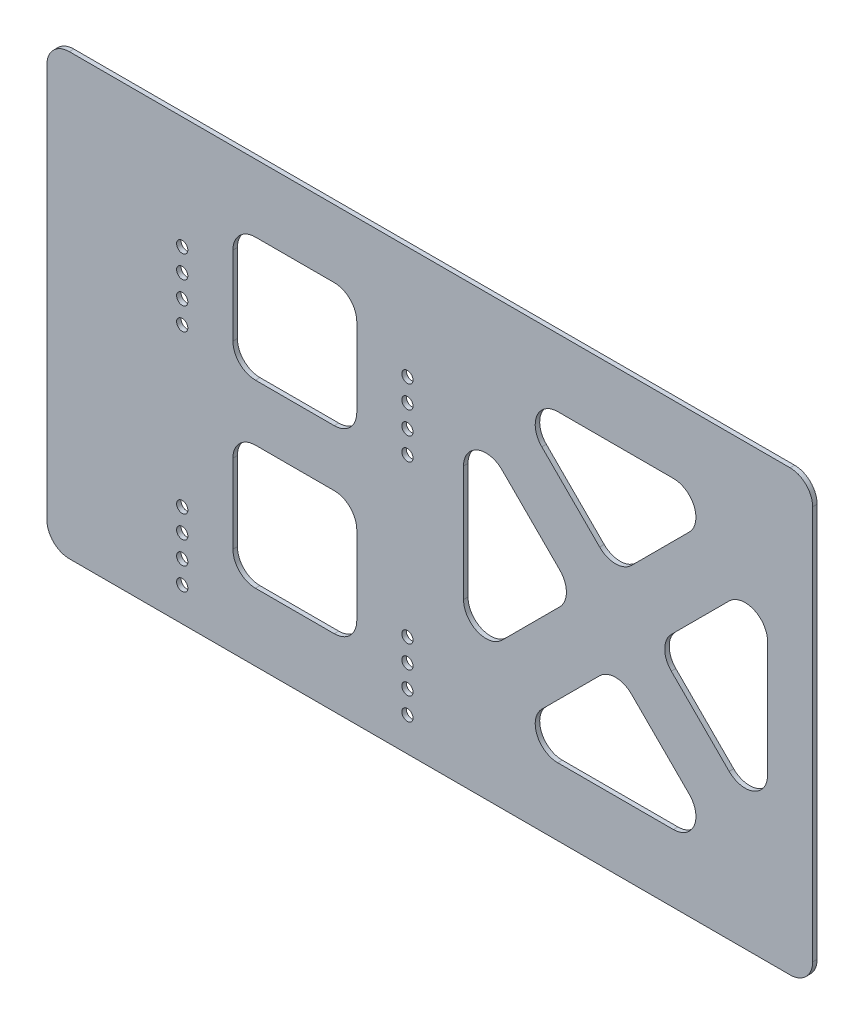
SolidWorks part; units mm, degrees
ref_plane "Front Plane" through (0, 0, 0) normal (0, 0, 1) x (1, 0, 0)
ref_plane "Top Plane" through (0, 0, 0) normal (0, 1, 0) x (1, 0, 0)
ref_plane "Right Plane" through (0, 0, 0) normal (1, 0, 0) x (0, 0, -1)
sketch "Sketch1" plane through (0, 0, 0) normal (0, 0, 1) x (1, 0, 0)
  line L0 (-269.9, 0) -> (-269.9, -1100) construction
  line L1 (-269.9, -292) -> (-609.9, -292)
  line L2 (-269.9, -292) -> (-269.9, -487)
  line L3 (-269.9, -487) -> (-609.9, -487)
  line L4 (-609.9, -292) -> (-609.9, -487)
  line L5 (-609.9, -1100) -> (-609.9, 0) construction
  line L6 (-589.9, -292) -> (-289.9, -292) construction
  dimension "D1" = 195
extrude "Boss-Extrude1" add sketch "Sketch1" along normal blind 2
sketch "Sketch2" plane through (0, 0, 2) normal (0, 0, 1) x (1, 0, 0)
  line L0 (-609.9, -412) -> (-269.9, -412) construction
  line L1 (-609.9, -292) -> (-609.9, -487) construction
  line L2 (-269.9, -487) -> (-269.9, -292) construction
  line L3 (-269.9, -292) -> (-609.9, -292) construction
  line L4 (-449.8, -487) -> (-449.8, -292) construction
  line L5 (-609.9, -487) -> (-269.9, -487) construction
  line L6 (-549.8, -292) -> (-549.8, -487) construction
  line L17 (-549.8, -292) -> (-449.8, -292) construction
  line L18 (-449.8, -462) -> (-549.8, -462) construction
  line L19 (-549.8, -462) -> (-549.8, -362) construction
  line L20 (-549.8, -362) -> (-449.8, -362) construction
  circle A0 centre (-449.8, -362) radius 2.5
  circle A1 centre (-449.8, -462) radius 2.5
  circle A2 centre (-549.8, -462) radius 2.5
  circle A3 centre (-549.8, -362) radius 2.5
  point P14 (-499.8, -292)
  point P21 (-549.8, -412)
  dimension "D4" = 5
  dimension "D1" = 120
  dimension "D2" = 100
  dimension "D3" = 110.1
extrude "Cut-Extrude1" cut sketch "Sketch2" against normal through all
pattern_linear "LPattern1" count 2 spacing 10 along (0, -1, 0) count 3 spacing 10 along (0, 1, 0) of "Cut-Extrude1"
sketch "Sketch3" plane through (0, 0, 2) normal (0, 0, 1) x (1, 0, 0)
  line L0 (-307.5777, -457) -> (-357.4, -407.1777)
  line L1 (-357.4, -407.1777) -> (-407.2223, -457)
  line L2 (-407.2223, -457) -> (-307.5777, -457)
  line L3 (-289.9, -439.3223) -> (-339.7223, -389.5)
  line L4 (-339.7223, -389.5) -> (-289.9, -339.6777)
  line L5 (-289.9, -339.6777) -> (-289.9, -439.3223)
  line L6 (-375.0777, -389.5) -> (-424.9, -439.3223)
  line L7 (-424.9, -439.3223) -> (-424.9, -339.6777)
  line L8 (-424.9, -339.6777) -> (-375.0777, -389.5)
  line L9 (-357.4, -371.8223) -> (-307.5777, -322)
  line L10 (-307.5777, -322) -> (-407.2223, -322)
  line L11 (-407.2223, -322) -> (-357.4, -371.8223)
  line L12 (-609.9, -487) -> (-269.9, -487) construction
  line L13 (-269.9, -292) -> (-609.9, -292) construction
  line L14 (-269.9, -487) -> (-269.9, -292) construction
  dimension "D1" = 25
  dimension "D2" = 25
  dimension "D3" = 30
  dimension "D4" = 30
  dimension "D5" = 20
extrude "Cut-Extrude2" cut sketch "Sketch3" against normal through all
sketch "Sketch4" plane through (0, 0, 2) normal (0, 0, 1) x (1, 0, 0)
  line L0 (-307.5777, -322) -> (-407.2223, -322) construction
  line L1 (-472.3, -457) -> (-527.3, -457)
  line L2 (-472.3, -457) -> (-472.3, -402)
  line L3 (-472.3, -402) -> (-527.3, -402)
  line L4 (-527.3, -457) -> (-527.3, -402)
  line L5 (-472.3, -322) -> (-527.3, -322)
  line L6 (-472.3, -322) -> (-472.3, -377)
  line L7 (-472.3, -377) -> (-527.3, -377)
  line L8 (-527.3, -322) -> (-527.3, -377)
  line L9 (-407.2223, -457) -> (-307.5777, -457) construction
  line L10 (-549.8, -472) -> (-549.8, -342) construction
  line L11 (-449.8, -472) -> (-449.8, -342) construction
  line L12 (-449.8, -342) -> (-472.3, -342) construction
  line L13 (-549.8, -342) -> (-527.3, -342) construction
  dimension "D1" = 25
extrude "Cut-Extrude3" cut sketch "Sketch4" against normal through all
fillet "Fillet1" radius 10 20 edges at (-527.3, -457, 1) (-527.3, -402, 1) (-472.3, -402, 1) (-472.3, -457, 1) (-472.3, -377, 1) (-472.3, -322, 1) (-527.3, -322, 1) (-527.3, -377, 1) (-339.7223, -389.5, 1) (-289.9, -439.3223, 1) (-289.9, -339.6777, 1) (-407.2223, -322, 1) (-357.4, -371.8223, 1) (-307.5777, -322, 1) (-375.0777, -389.5, 1) (-424.9, -439.3223, 1) (-424.9, -339.6777, 1) (-357.4, -407.1777, 1) (-407.2223, -457, 1) (-307.5777, -457, 1)
fillet "Fillet2" radius 10 4 edges at (-609.9, -292, 1) (-269.9, -292, 1) (-269.9, -487, 1) (-609.9, -487, 1)
